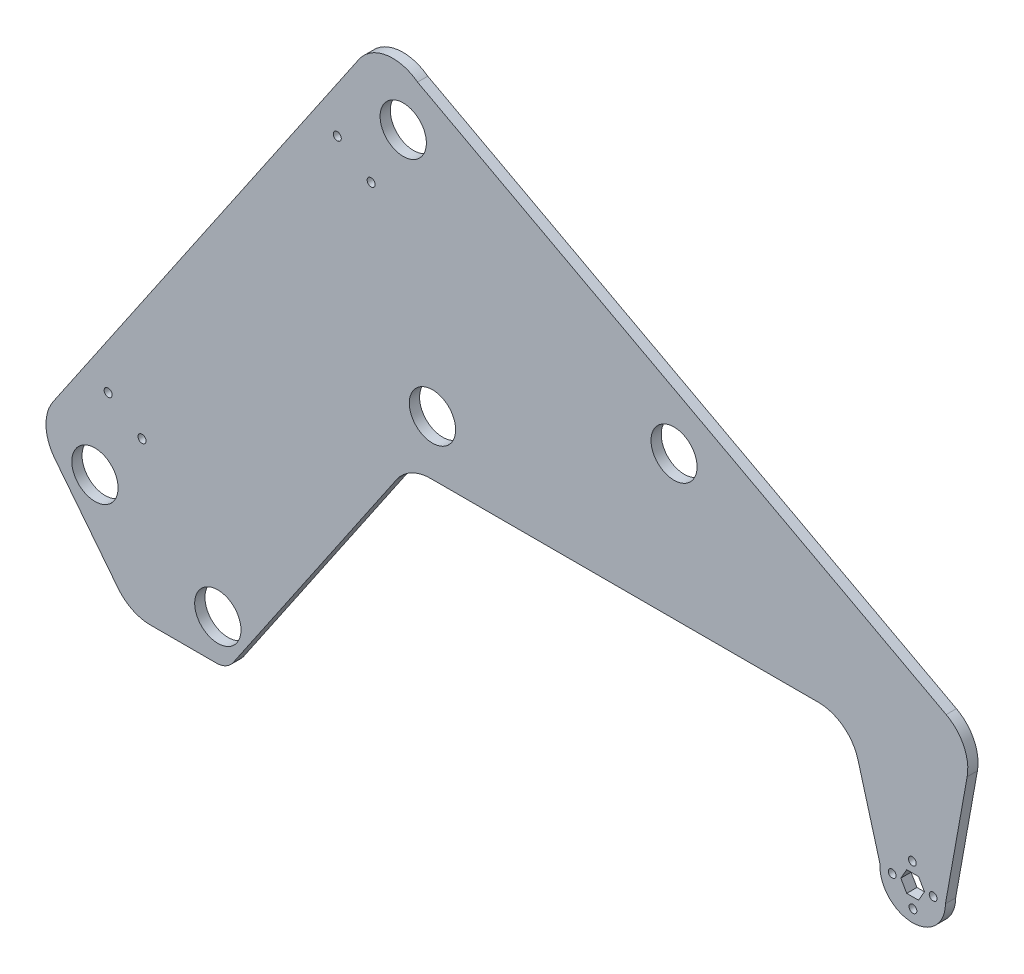
SolidWorks part; units mm, degrees
other "Markup1"
sketch "Sketch1" plane through (-441.7893, 331.8239, 6.35) normal (-0.0431, 0.0102, 0.999) x (0.9985, 0.0354, 0.0427)
sketch "Sketch2" plane through (-413.6701, 343.933, 6.35) normal (-0.0431, 0.0102, 0.999) x (0.9985, 0.0354, 0.0427)
sketch "Sketch3" plane through (-436.3774, 318.5567, 6.35) normal (-0.0431, 0.0102, 0.999) x (0.9985, 0.0354, 0.0427)
sketch "Sketch5" plane through (-436.3774, 318.5567, 6.35) normal (-0.0431, 0.0102, 0.999) x (0.9985, 0.0354, 0.0427)
sketch "Sketch7" plane through (-430.3226, 318.5567, 6.35) normal (-0.0431, 0.0102, 0.999) x (0.9985, 0.0354, 0.0427)
sketch "Sketch9" plane through (-430.3226, 318.5567, 6.35) normal (-0.0431, 0.0102, 0.999) x (0.9985, 0.0354, 0.0427)
sketch "Sketch11" plane through (-430.3226, 318.5567, 6.35) normal (-0.0431, 0.0102, 0.999) x (0.9985, 0.0354, 0.0427)
sketch "Sketch13" plane through (-430.3226, 318.5567, 6.35) normal (-0.0431, 0.0102, 0.999) x (0.9985, 0.0354, 0.0427)
sketch "Sketch15" plane through (-430.3226, 318.5567, 6.35) normal (-0.0431, 0.0102, 0.999) x (0.9985, 0.0354, 0.0427)
sketch "Sketch19" plane through (-430.3226, 318.5567, 6.35) normal (-0.0431, 0.0102, 0.999) x (0.9985, 0.0354, 0.0427)
sketch "Sketch19" plane through (-430.3226, 318.5567, 6.35) normal (-0.0431, 0.0102, 0.999) x (0.9985, 0.0354, 0.0427)
sketch "Sketch21" plane through (-430.3226, 318.5567, 6.35) normal (-0.0431, 0.0102, 0.999) x (0.9985, 0.0354, 0.0427)
sketch "Sketch23" plane through (-430.3226, 318.5567, 6.35) normal (-0.0431, 0.0102, 0.999) x (0.9985, 0.0354, 0.0427)
sketch "Sketch25" plane through (-430.3226, 318.5567, 6.35) normal (-0.0431, 0.0102, 0.999) x (0.9985, 0.0354, 0.0427)
sketch "Sketch27" plane through (-430.3226, 318.5567, 6.35) normal (-0.0431, 0.0102, 0.999) x (0.9985, 0.0354, 0.0427)
sketch "Sketch29" plane through (-430.3226, 318.5567, 6.35) normal (-0.0431, 0.0102, 0.999) x (0.9985, 0.0354, 0.0427)
sketch "Sketch31" plane through (-430.3226, 318.5567, 6.35) normal (-0.0431, 0.0102, 0.999) x (0.9985, 0.0354, 0.0427)
sketch "Sketch33" plane through (-430.3226, 318.5567, 6.35) normal (-0.0431, 0.0102, 0.999) x (0.9985, 0.0354, 0.0427)
other "Markup2"
sketch "Sketch4" plane through (102.4721, 318.5567, 6.35) normal (0.9364, 0.1073, 0.3342) x (0.3416, -0.0598, -0.9379)
sketch "Sketch6" plane through (102.4721, 318.5567, 6.35) normal (0.9364, 0.1073, 0.3342) x (0.3416, -0.0598, -0.9379)
sketch "Sketch8" plane through (141.2086, 318.5567, 6.35) normal (0.9364, 0.1073, 0.3342) x (0.3416, -0.0598, -0.9379)
sketch "Sketch10" plane through (141.2086, 318.5567, 6.35) normal (0.9364, 0.1073, 0.3342) x (0.3416, -0.0598, -0.9379)
sketch "Sketch12" plane through (141.2086, 318.5567, 6.35) normal (0.9364, 0.1073, 0.3342) x (0.3416, -0.0598, -0.9379)
sketch "Sketch14" plane through (141.2086, 318.5567, 6.35) normal (0.9364, 0.1073, 0.3342) x (0.3416, -0.0598, -0.9379)
sketch "Sketch16" plane through (141.2086, 318.5567, 6.35) normal (0.9364, 0.1073, 0.3342) x (0.3416, -0.0598, -0.9379)
sketch "Sketch20" plane through (141.2086, 318.5567, 6.35) normal (0.9364, 0.1073, 0.3342) x (0.3416, -0.0598, -0.9379)
sketch "Sketch20" plane through (141.2086, 318.5567, 6.35) normal (0.9364, 0.1073, 0.3342) x (0.3416, -0.0598, -0.9379)
sketch "Sketch22" plane through (141.2086, 318.5567, 6.35) normal (0.9364, 0.1073, 0.3342) x (0.3416, -0.0598, -0.9379)
sketch "Sketch24" plane through (141.2086, 318.5567, 6.35) normal (0.9364, 0.1073, 0.3342) x (0.3416, -0.0598, -0.9379)
sketch "Sketch26" plane through (141.2086, 318.5567, 6.35) normal (0.9364, 0.1073, 0.3342) x (0.3416, -0.0598, -0.9379)
sketch "Sketch28" plane through (141.2086, 318.5567, 6.35) normal (0.9364, 0.1073, 0.3342) x (0.3416, -0.0598, -0.9379)
sketch "Sketch30" plane through (141.2086, 318.5567, 6.35) normal (0.9364, 0.1073, 0.3342) x (0.3416, -0.0598, -0.9379)
sketch "Sketch32" plane through (141.2086, 318.5567, 6.35) normal (0.9364, 0.1073, 0.3342) x (0.3416, -0.0598, -0.9379)
sketch "Sketch34" plane through (141.2086, 318.5567, 6.35) normal (0.9364, 0.1073, 0.3342) x (0.3416, -0.0598, -0.9379)
material "Lexan"
ref_plane "Front Plane" through (0, 0, 0) normal (0, 0, 1) x (1, 0, 0)
ref_plane "Top Plane" through (0, 0, 0) normal (0, 1, 0) x (1, 0, 0)
ref_plane "Right Plane" through (0, 0, 0) normal (1, 0, 0) x (0, 0, -1)
sketch "Model" plane through (0, 0, 0) normal (0, 0, 1) x (1, 0, 0)
  line L1 (-191.9011, 104.6502) -> (-112.96, 104.6502)
  line L3 (-314.2383, -55.3595) -> (-212.8994, 93.5413)
  line L4 (-236.3032, 307.4477) -> (-425.9209, 28.8361)
  line L5 (-424.8981, -1.1437) -> (-385.5815, -51.2028)
  line L13 (114.3386, 35.8116) -> (110.6724, 42.1616)
  line L14 (110.6724, 42.1616) -> (103.3401, 42.1616)
  line L15 (103.3401, 42.1616) -> (99.6739, 35.8116)
  line L16 (99.6739, 35.8116) -> (103.3401, 29.4616)
  line L17 (103.3401, 29.4616) -> (110.6724, 29.4616)
  line L18 (110.6724, 29.4616) -> (114.3386, 35.8116)
  line L19 (-365.606, -60.914) -> (-324.7375, -60.914)
  line L20 (-871.0211, -88.854) -> (370.1019, -88.854) construction
  line L22 (127.3262, 35.8116) -> (140.8079, 110.8095)
  line L28 (-399.9752, 2.586) -> (-323.7752, -35.514) construction
  line L29 (-323.7752, -35.514) -> (-190.7071, 138.5169) construction
  line L30 (-190.7071, 138.5169) -> (-208.8329, 283.4378) construction
  line L31 (-208.8329, 283.4378) -> (-399.9752, 2.586) construction
  line L32 (86.727, 37.0982) -> (73.1352, 86.0462)
  line L33 (48.6612, 104.6502) -> (-11.3966, 104.6502)
  line L34 (106.8234, 42.1616) -> (106.8234, 48.5116)
  line L35 (127.8091, 137.6897) -> (-86.3327, 252.4836)
  line L36 (-112.96, 104.6502) -> (-68.51, 104.6502)
  line L37 (-122.3008, 271.7648) -> (-85.2777, 251.9181)
  line L38 (-156.701, 288.2074) -> (-155.3641, 287.4328)
  line L39 (-49.867, 219.9669) -> (-44.4668, 230.0407)
  line L40 (-68.51, 104.6502) -> (-2.1388, 104.6502)
  line L41 (-122.3008, 271.7648) -> (-199.9496, 313.3896)
  line L42 (-208.8329, 283.4378) -> (-40.9355, 193.4339) construction
  line L44 (-199.9496, 313.3896) -> (-165.7592, 287.0167)
  line L45 (-155.3641, 287.4328) -> (-154.5079, 289.0299)
  arc A3 (106.824, 42.1589) -> (106.8234, 42.1616) centre (81.3892, 35.8116) ccw
  circle A9 centre (-323.7752, -35.514) radius 14.351
  circle A10 centre (-399.9752, 2.586) radius 14.351
  circle A12 centre (-190.7071, 138.5169) radius 14.351
  arc A21 (-191.9011, 104.6502) -> (-212.8994, 93.5413) centre (-191.9011, 79.2502) ccw
  circle A22 centre (-208.8329, 283.4378) radius 14.351
  circle A24 centre (107.0062, 35.8116) radius 6.35 construction
  arc A31 (-324.7375, -60.914) -> (-314.2383, -55.3595) centre (-324.7375, -48.214) ccw
  arc A44 (-236.3032, 307.4477) -> (-199.9496, 313.3896) centre (-215.305, 293.1567) cw
  arc A45 (-365.606, -60.914) -> (-385.5815, -51.2028) centre (-365.606, -35.514) cw
  arc A46 (73.1352, 86.0462) -> (48.6612, 104.6502) centre (48.6612, 79.2502) ccw
  arc A47 (140.8079, 110.8095) -> (127.8091, 137.6897) centre (115.8086, 115.3033) ccw
  arc A48 (-424.8981, -1.1437) -> (-425.9209, 28.8361) centre (-404.9226, 14.5451) cw
  circle A50 centre (-51.0071, 217.8402) radius 2.413 construction
  circle A52 centre (-67.7968, 226.8406) radius 2.413 construction
  circle A53 centre (-166.8993, 284.89) radius 2.413 construction
  circle A55 centre (-175.8997, 268.1002) radius 2.413 construction
  circle A56 centre (-171.3995, 276.4951) radius 2.413 [skipped]
  circle A57 centre (-59.4019, 222.3404) radius 2.413 [skipped]
  arc A58 (86.727, 37.0982) -> (127.3262, 35.8116) centre (107.0062, 35.8116) ccw
  circle A65 centre (106.8234, 48.5116) radius 2.413
  circle A66 centre (119.7062, 35.9944) radius 2.413
  circle A67 centre (107.1891, 23.1116) radius 2.413
  circle A68 centre (94.3062, 35.6287) radius 2.413
  circle A69 centre (-40.9355, 193.4339) radius 14.2875
  ellipse E0 centre (-551.1692, 173.9527) end of major axis (-591.2054, 216.0961) minor radius 17.278
  point P31 (-177.5612, 330.9695)
  point P43 (-377.9543, -60.914)
  point P60 (-205.3388, 104.6502)
  point P64 (-436.3774, 13.472)
  point P75 (107.0062, 35.8116)
  point P83 (107.0062, 35.8116)
  dimension "D3" = 38.1
  dimension "D5" = 76.2
  dimension "D6" = 40.64
  dimension "D7" = 6.35
  dimension "D8" = 28.702
  dimension "D11" = 139.7
  dimension "D12" = 27.94
  dimension "D21" = 124.238
  dimension "D13" = 12.7
  dimension "D16" = 355.6
  dimension "D23" = 242.9699
  dimension "D24" = 76.2
  dimension "D26" = 28.575
  dimension "D14" = 50.8
  dimension "D20" = 254
  dimension "D29" = 25.4
  dimension "D31" = 25.4
  dimension "D25" = 190.5
  dimension "D32" = 25.4
  dimension "D33" = 25.4
  dimension "D34" = 176.784
  dimension "D35" = 19.05
  dimension "D37" = 3
  dimension "D36" = 4.826
  dimension "D41" = 4.826
  dimension "D43" = 19.05
  dimension "D19" = 4.826
  dimension "D9" = 19.05
  dimension "D10" = 146.05
  dimension "D15" = 33.8667
  dimension "D17" = 339.725
  dimension "D18" = 219.075
  dimension "D22" = 25.4
  dimension "D27" = 53.2168
  dimension "D39" = 11.43
  dimension ".3" = 11.43
  dimension "D40" = 43.18
  dimension "D42" = 3
extrude "Boss-Extrude1" add sketch "Model" along normal blind 6.35
sketch "Sketch35" plane through (0, 0, 6.35) normal (0, 0, 1) x (1, 0, 0)
  line L0 (-370.7859, 36.4881) -> (-391.7841, 50.7791) construction
  line L1 (-391.7841, 50.7791) -> (-249.7315, 259.5019) construction
  line L2 (-249.7315, 259.5019) -> (-228.7332, 245.2108) construction
  line L3 (-228.7332, 245.2108) -> (-370.7859, 36.4881) construction
  line L4 (-236.3032, 307.4477) -> (-425.9209, 28.8361) construction
  circle A0 centre (-391.7841, 50.7791) radius 2.4892
  circle A1 centre (-249.7315, 259.5019) radius 2.4892
  circle A2 centre (-228.7332, 245.2108) radius 2.4892
  circle A3 centre (-370.7859, 36.4881) radius 2.4892
  circle A4 centre (-399.9752, 2.586) radius 14.351 construction
  dimension "D3" = 4.9784
  dimension "D1" = 44.45
  dimension "D2" = 252.476
  dimension "D4" = 25.4
  dimension "D5" = 15.875
extrude "Cut-Extrude1" cut sketch "Sketch35" against normal up to next
